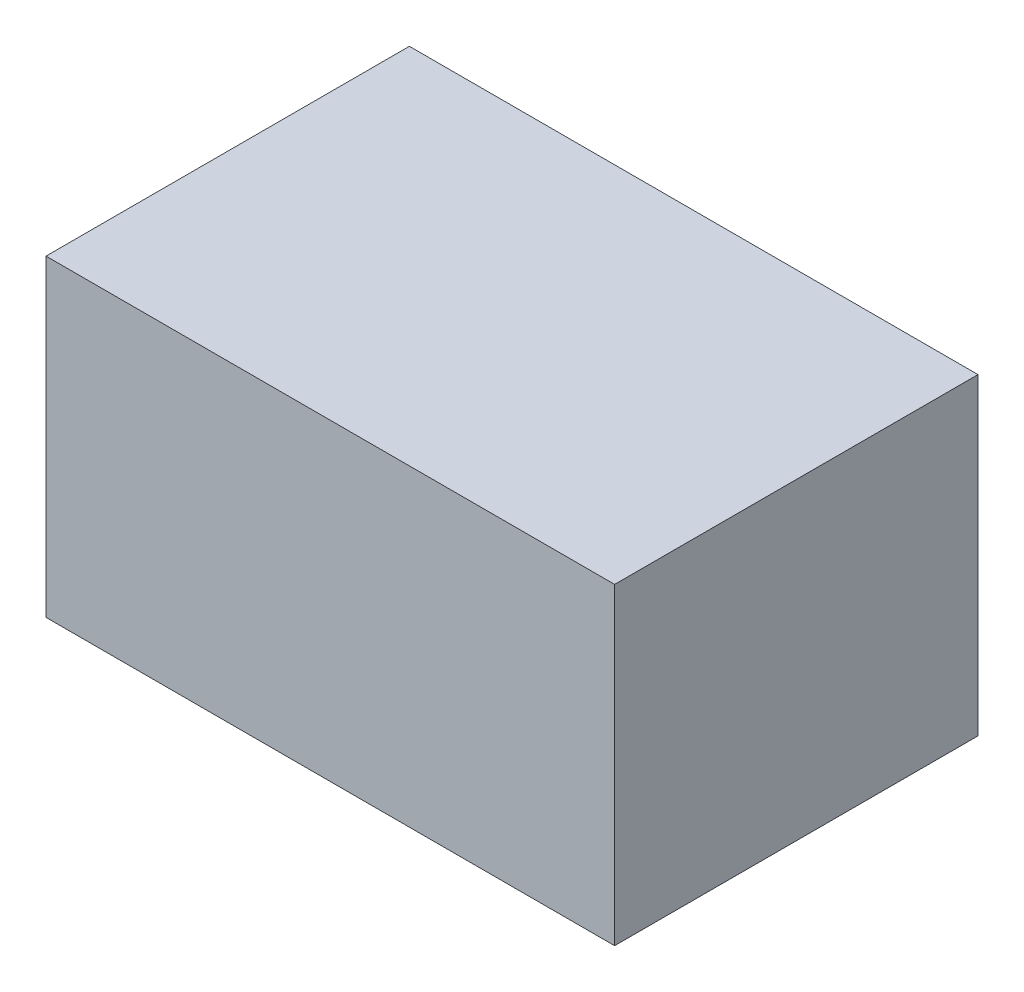
SolidWorks part; units mm, degrees
ref_plane "Front Plane" through (0, 0, 0) normal (0, 0, 1) x (1, 0, 0)
ref_plane "Top Plane" through (0, 0, 0) normal (0, 1, 0) x (1, 0, 0)
ref_plane "Right Plane" through (0, 0, 0) normal (1, 0, 0) x (0, 0, -1)
sketch "Sketch1" plane through (0, 0, 0) normal (0, 1, 0) x (1, 0, 0)
  line L1 (0, 0) -> (84.5, 0)
  line L2 (0, 0) -> (0, 54)
  line L3 (0, 54) -> (84.5, 54)
  line L4 (84.5, 0) -> (84.5, 54)
  dimension "D1" = 84.5
  dimension "D2" = 54
extrude "Boss-Extrude2" add sketch "Sketch1" along normal blind 46.5
